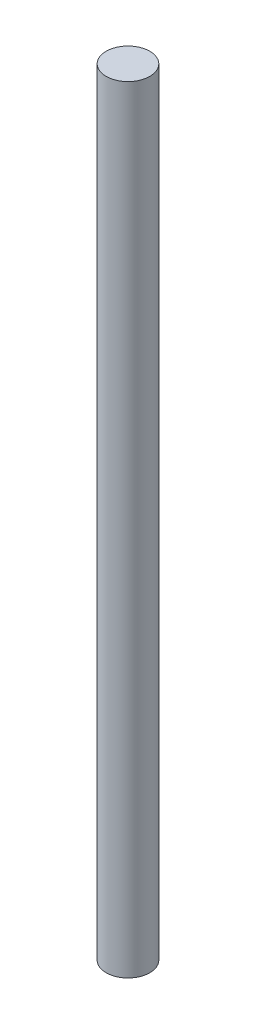
SolidWorks part; units mm, degrees
ref_plane "Front Plane" through (0, 0, 0) normal (0, 0, 1) x (1, 0, 0)
ref_plane "Top Plane" through (0, 0, 0) normal (0, 1, 0) x (1, 0, 0)
ref_plane "Right Plane" through (0, 0, 0) normal (1, 0, 0) x (0, 0, -1)
sketch "Sketch1" plane through (0, 0, 0) normal (0, 1, 0) x (1, 0, 0)
  circle A0 centre (0, 0) radius 3.175
  dimension "D1" = 6.35
extrude "Boss-Extrude1" add sketch "Sketch1" along normal blind 113.03
